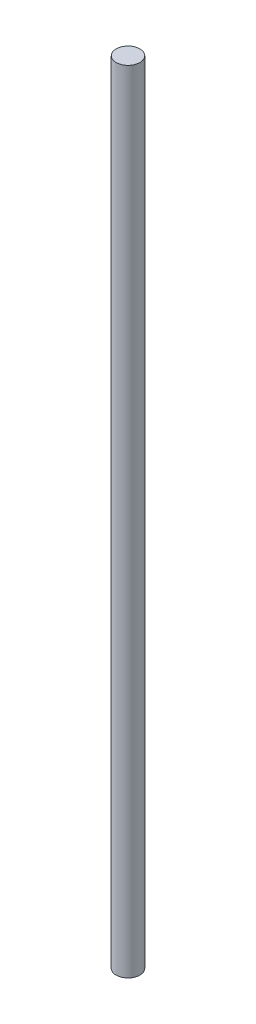
SolidWorks part; units mm, degrees
ref_plane "Спереди" through (0, 0, 0) normal (0, 0, 1) x (1, 0, 0)
ref_plane "Сверху" through (0, 0, 0) normal (0, 1, 0) x (1, 0, 0)
ref_plane "Справа" through (0, 0, 0) normal (1, 0, 0) x (0, 0, -1)
sketch "Эскиз2" plane through (0, 0, 0) normal (0, 1, 0) x (1, 0, 0)
  circle A0 centre (0, 0) radius 1.5
  dimension "D1" = 3
extrude "Бобышка-Вытянуть1" add sketch "Эскиз2" along normal blind 100
